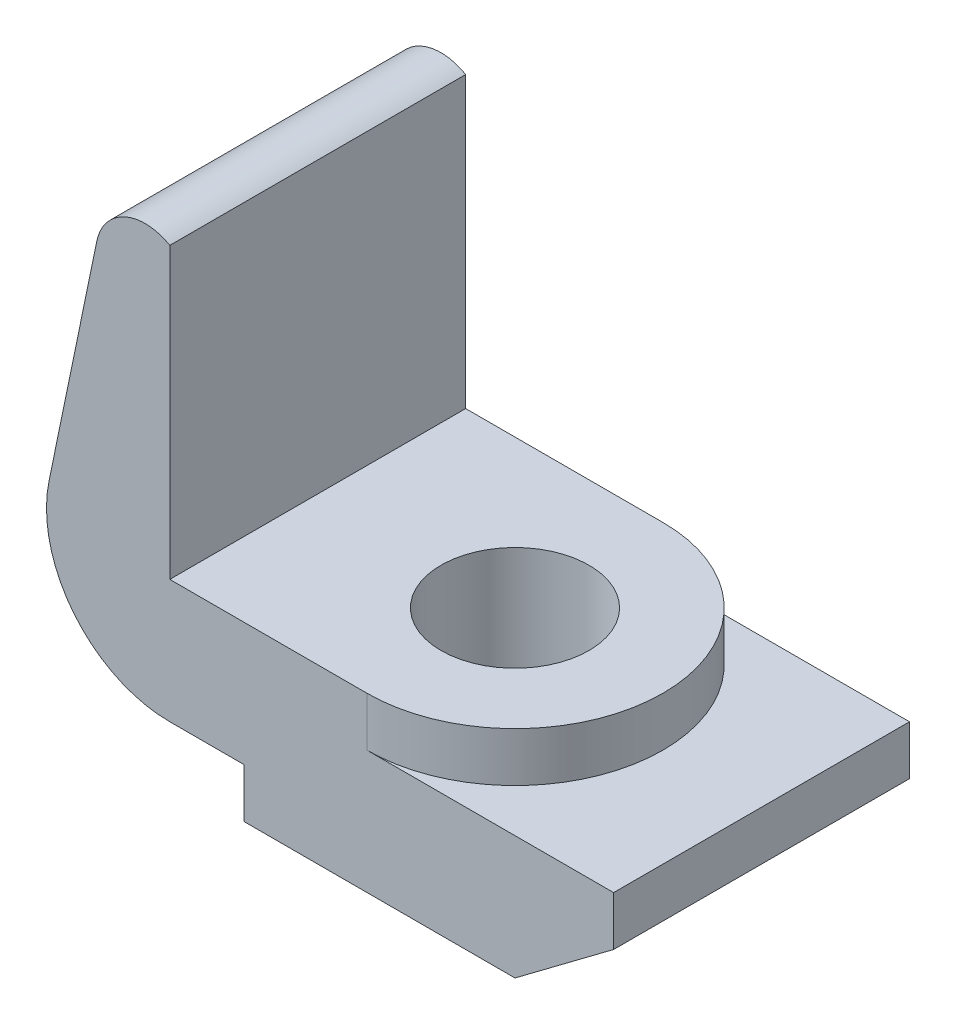
SolidWorks part; units mm, degrees
ref_plane "Front Plane" through (0, 0, 0) normal (0, 0, 1) x (1, 0, 0)
ref_plane "Top Plane" through (0, 0, 0) normal (0, 1, 0) x (1, 0, 0)
ref_plane "Right Plane" through (0, 0, 0) normal (1, 0, 0) x (0, 0, -1)
sketch "Sketch1" plane through (0, 0, 0) normal (0, 0, 1) x (1, 0, 0)
  line L0 (0, 76.2) -> (0, 0)
  line L1 (0, 0) -> (50.8, 0)
  line L2 (50.8, 0) -> (50.8, -12.7)
  line L3 (50.8, -12.7) -> (114.3, -12.7)
  line L4 (114.3, -12.7) -> (114.3, -25.4)
  line L5 (114.3, -25.4) -> (88.9, -44.45)
  line L6 (88.9, -44.45) -> (19.05, -44.45)
  line L7 (19.05, -44.45) -> (19.05, -31.75)
  line L8 (19.05, -31.75) -> (0, -31.75)
  line L9 (0, 76.2) -> (-6.35, 76.2)
  line L10 (-18.788, 66.0662) -> (-31.0951, 6.4155)
  circle A0 centre (0, 0) radius 31.75
  circle A1 centre (-6.35, 63.5) radius 12.7
  point P14 (33.6722, 128.7801)
  point P15 (5.0199, 42.3977)
  point P18 (46.4832, 22.5028)
  point P19 (25.6358, 77.3533)
  point P20 (26.6131, 75.4103)
  point P21 (26.9954, 78.1415)
  point P22 (16.3886, 18.0018)
  point P23 (0, 0)
  point P25 (-25.2992, 65.4115)
  point P27 (-17.0367, 62.7641)
  point P28 (-18.6329, 63.4196)
  point P29 (-6.35, 63.5)
  point P30 (-6.35, 63.5)
  point P31 (-9.3958, 63.5)
  point P32 (-6.35, 63.5)
  point P33 (-6.35, 63.5)
  point P34 (-4.7107, 63.5)
  point P35 (-26.2357, 63.5)
  point P36 (-6.35, 63.5)
  point P37 (-2.7637, 63.5)
  point P38 (0, 0)
  point P39 (0, 0)
  point P40 (0, 0)
  dimension "D4" = 25.4
  dimension "D7" = 50.8
  dimension "D1" = 76.2
  dimension "D2" = 69.85
  dimension "D3" = 6.35
  dimension "D5" = 120.65
  dimension "D6" = 31.75
  dimension "D8" = 114.3
  dimension "D9" = 12.7
  dimension "D10" = 19.05
  dimension "D11" = 12.7
extrude "Boss-Extrude1" add sketch "Sketch1" along normal blind 76.2 contours L0 A0 L1 | A1 L10 A0 L0 | L0 A1 | A0 L8 L7 L6 L5 L4 L3 L2 L1
sketch "Sketch2" plane through (0, -12.7, 0) normal (0, 1, 0) x (1, 0, 0)
  line L0 (50.8, -76.2) -> (50.8, 0) construction
  circle A0 centre (50.8, -38.1) radius 38.1
extrude "Boss-Extrude2" add sketch "Sketch2" along normal up to surface (12.7 mm away) up to face at (25.4, 0, 38.1)
hole_wizard "3/4 (1.5) Diameter Hole1" positions "Sketch3" profile "Sketch4" hole size "3/4" standard "ANSI Inch" end condition through all
sketch "Sketch3" plane through (0, 0, 0) normal (0, 1, 0) x (1, 0, 0)
  point P0 (50.8, -38.1)
sketch "Sketch4" plane through (50.8, 0, 38.1) normal (1, 0, 0) x (0, 0, 1)
  line L0 (0, 0) -> (0, 44.45)
  line L1 (0, 44.45) -> (19.05, 44.45)
  line L2 (19.05, 44.45) -> (19.05, 0)
  line L5 (19.05, 0) -> (0, 0)
  line L11 (0, -6.35) -> (0, 107.95) construction
  dimension "Thru Hole Dia." = 38.1
  dimension "Thru Hole Depth" = 44.45
